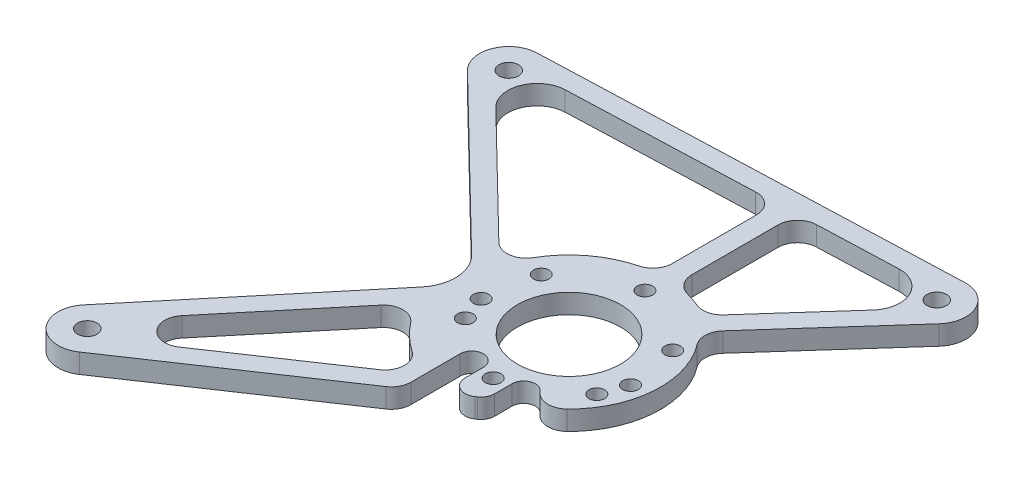
SolidWorks part; units mm, degrees
material "7050-T73510"
ref_plane "Płaszczyzna przednia" through (0, 0, 0) normal (0, 0, 1) x (1, 0, 0)
ref_plane "Płaszczyzna górna" through (0, 0, 0) normal (0, 1, 0) x (1, 0, 0)
ref_plane "Płaszczyzna prawa" through (0, 0, 0) normal (1, 0, 0) x (0, 0, -1)
sketch "Szkic3" plane through (0, 0, 0) normal (0, 1, 0) x (1, 0, 0)
  line L1 (-1915.5489, -140.9908) -> (-1703.3489, -133.2209)
  line L2 (-1750, -223.5762) -> (-1691.6125, -158.2029)
  line L3 (-1899.9755, -391.673) -> (-1768.1213, -302.9041)
  line L5 (-1842.3877, -247.6752) -> (-1925.468, -166.7241)
  line L10 (-1919.8833, -369.6363) -> (-1840.9708, -274.7914)
  line L11 (-1685.3, -117.9) -> (-1702.8, -148.2109) construction
  line L12 (-1507.3807, -117.9) -> (-1863.2193, -117.9) construction
  line L13 (-2061.0869, -130) -> (-1798.9131, -130) construction
  line L14 (-1915, -155.9808) -> (-1930, -130) construction
  circle A2 centre (-1930, -130) radius 12.5
  circle A3 centre (-1685.3, -117.9) radius 12.5
  arc A5 (-1750, -223.5762) -> (-1768.1213, -302.9041) centre (-1782, -258) cw
  circle A6 centre (-1782, -258) radius 26.5
  arc A8 (-1925.468, -166.7241) -> (-1915.5489, -140.9908) centre (-1915, -155.9808) cw
  arc A9 (-1691.6125, -158.2029) -> (-1703.3489, -133.2209) centre (-1702.8, -148.2109) ccw
  circle A10 centre (-1930, -400) radius 12.5
  arc A11 (-1919.8833, -369.6363) -> (-1899.9755, -391.673) centre (-1908.3525, -379.2301) ccw
  arc A20 (-1840.9708, -274.7914) -> (-1842.3877, -247.6752) centre (-1856.3451, -261.9997) ccw
  point P17 (-1685.3, -117.9)
  point P25 (-1930, -130)
  dimension "D4" = 47
  dimension "D7" = 25
  dimension "D10" = 25
  dimension "D11" = 53
  dimension "D12" = 15
  dimension "D5" = 1782
  dimension "D18" = 25
  dimension "D20" = 15
  dimension "D13" = 15
  dimension "D19" = 30
  dimension "D23" = 270
  dimension "D27" = 30
  dimension "D3" = 1930
  dimension "D14" = 130
  dimension "D15" = 1930
  dimension "D21" = 20
  dimension "D28" = 121.2301
  dimension "D6" = 258
  dimension "D8" = 117.9
  dimension "D9" = 1685.3
  dimension "D16" = 32
  dimension "D17" = 74.3451
  dimension "D22" = 60
  dimension "D24" = 35
  dimension "D25" = 117.9755
  dimension "D26" = 137.8833
  dimension "D29" = 60
extrude "Dodanie-wyciągnięcie1" add sketch "Szkic3" along normal blind 10
hole_wizard "Otwór1" positions "Szkic4" profile "Szkic5" legacy end condition up to next
sketch "Szkic4" plane through (0, 0, 0) normal (0, -1, 0) x (-1, 0, 0)
  circle A0 centre (1782, -258) radius 26.5 construction
  circle A1 centre (1782, -258) radius 26.5
  point P0 (1782, -219)
  dimension "D1" = 39
sketch "Szkic5" plane through (-1782, 0, 219) normal (1, 0, 0) x (0, 0, -1)
  line L0 (0, 0) -> (0, 10.001)
  line L1 (0, 10.001) -> (4, 10.001)
  line L2 (4, 10.001) -> (4, 0)
  line L3 (4, 0) -> (0, 0)
  line L4 (0, 110) -> (0, -10) construction
  dimension "Średnica" = 8
  dimension "Głębokość" = 10.001
pattern_circular "Szyk kołowy1" count 18 over 360 about axis through (-1782, 10, 258) along (0, -1, 0) skipping 1, 2, 4, 7, 8, 10, 11, 14, 16, 17 of "Otwór1"
hole_wizard "Otwór2" positions "Szkic8" profile "Szkic9" legacy
sketch "Szkic8" plane through (0, 0, 0) normal (0, -1, 0) x (-1, 0, 0)
  arc A0 (1703.3489, -133.2209) -> (1691.6125, -158.2029) centre (1702.8, -148.2109) ccw construction
  point P0 (1702.8, -148.2109)
sketch "Szkic9" plane through (-1702.8, 0, 148.2109) normal (1, 0, 0) x (0, 0, -1)
  line L0 (0, 0) -> (0, 100)
  line L1 (0, 100) -> (5, 100)
  line L2 (5, 100) -> (5, 0)
  line L3 (5, 0) -> (0, 0)
  line L4 (0, 110) -> (0, -10) construction
  dimension "Średnica" = 10
  dimension "Głębokość" = 100
hole_wizard "Otwór3" positions "Szkic10" profile "Szkic11" legacy
sketch "Szkic10" plane through (0, 0, 0) normal (0, -1, 0) x (-1, 0, 0)
  arc A0 (1925.468, -166.7241) -> (1915.5489, -140.9908) centre (1915, -155.9808) ccw construction
  point P0 (1915, -155.9808)
sketch "Szkic11" plane through (-1915, 0, 155.9808) normal (1, 0, 0) x (0, 0, -1)
  line L0 (0, 0) -> (0, 100)
  line L1 (0, 100) -> (5, 100)
  line L2 (5, 100) -> (5, 0)
  line L3 (5, 0) -> (0, 0)
  line L4 (0, 110) -> (0, -10) construction
  dimension "Średnica" = 10
  dimension "Głębokość" = 100
hole_wizard "Otwór4" positions "Szkic12" profile "Szkic13" legacy end condition up to next
sketch "Szkic12" plane through (0, 0, 0) normal (0, -1, 0) x (-1, 0, 0)
  arc A0 (1899.9755, -391.673) -> (1919.8833, -369.6363) centre (1908.3525, -379.2301) ccw construction
  point P0 (1908.3525, -379.2301)
sketch "Szkic13" plane through (-1908.3525, 0, 379.2301) normal (1, 0, 0) x (0, 0, -1)
  line L0 (0, 0) -> (0, 10)
  line L1 (0, 10) -> (5, 10)
  line L2 (5, 10) -> (5, 0)
  line L3 (5, 0) -> (0, 0)
  line L4 (0, 110) -> (0, -10) construction
  dimension "Średnica" = 10
  dimension "Głębokość" = 10
sketch "Szkic14" plane through (0, 0, 0) normal (0, -1, 0) x (-1, 0, 0)
  line L0 (1830.3878, -245.4055) -> (1901.7597, -175.8627)
  line L1 (1787, -208.2506) -> (1787, -146.2906)
  line L2 (1787, -146.2906) -> (1891.8406, -150.1294)
  line L3 (1777, -208.2506) -> (1777, -145.9244)
  line L4 (1777, -145.9244) -> (1726.4495, -144.0735)
  line L5 (1756.0056, -215.2883) -> (1714.7132, -169.0554)
  line L6 (1915.5489, -140.9908) -> (1703.3489, -133.2209) construction
  line L7 (1889.8509, -349.1755) -> (1834.501, -282.6505)
  line L8 (1750, -223.5762) -> (1691.6125, -158.2029) construction
  line L9 (1876.5791, -363.8666) -> (1800.8187, -312.8621)
  line L10 (1925.468, -166.7241) -> (1842.3877, -247.6752) construction
  line L11 (1899.9755, -391.673) -> (1768.1213, -302.9041) construction
  line L12 (1919.8833, -369.6363) -> (1840.9708, -274.7914) construction
  arc A0 (1830.3878, -245.4055) -> (1787, -208.2506) centre (1782, -258) ccw
  arc A1 (1901.7597, -175.8627) -> (1891.8406, -150.1294) centre (1891.2917, -165.1194) ccw
  arc A2 (1714.7132, -169.0554) -> (1726.4495, -144.0735) centre (1725.9007, -159.0634) cw
  arc A3 (1756.0056, -215.2883) -> (1777, -208.2506) centre (1782, -258) cw
  circle A4 centre (1782, -258) radius 26.5 construction
  circle A5 centre (1782, -258) radius 26.5 construction
  arc A8 (1834.501, -282.6505) -> (1800.8187, -312.8621) centre (1782, -258) cw
  arc A9 (1889.8509, -349.1755) -> (1876.5791, -363.8666) centre (1882.1637, -355.5714) cw
  dimension "D2" = 50
  dimension "D3" = 50
  dimension "D11" = 58
  dimension "D14" = 10
  dimension "D9" = 15
  dimension "D10" = 15
  dimension "D1" = 10
  dimension "D4" = 10
  dimension "D5" = 10
  dimension "D6" = 5
  dimension "D7" = 10
  dimension "D8" = 10
  dimension "D12" = 10
  dimension "D13" = 10
extrude "Wytnij-wyciągnięcie1" cut sketch "Szkic14" against normal through all
fillet "Zaokrąglenie1" radius 10 10 edges at (-1756.0056, 5, 215.2883) (-1787, 5, 208.2506) (-1777, 5, 208.2506) (-1787, 5, 146.2906) (-1777, 5, 145.9244) (-1834.501, 5, 282.6505) (-1768.1213, 5, 302.9041) (-1830.3878, 5, 245.4055) (-1800.8187, 5, 312.8621) (-1750, 5, 223.5762)
hole_wizard "Otwór5" positions "Szkic15" profile "Szkic16" legacy end condition up to next
sketch "Szkic15" plane through (0, 0, 0) normal (0, -1, 0) x (-1, 0, 0)
  point P0 (1795.3388, -294.648)
  point P2 (1768.6612, -294.648)
sketch "Szkic16" plane through (-1795.3388, 0, 294.648) normal (1, 0, 0) x (0, 0, -1)
  line L0 (0, 0) -> (0, 10)
  line L1 (0, 10) -> (5, 10)
  line L2 (5, 10) -> (5, 0)
  line L3 (5, 0) -> (0, 0)
  line L4 (0, 110) -> (0, -10) construction
  dimension "Średnica" = 10
  dimension "Głębokość" = 10
sketch "Szkic18" plane through (0, 0, 0) normal (0, -1, 0) x (-1, 0, 0)
  line L0 (1762.6612, -294.648) -> (1762.6612, -300.837)
  line L1 (1774.6612, -294.648) -> (1774.6612, -307.3071)
  line L2 (1789.3388, -294.648) -> (1789.3388, -317.1885)
  line L3 (1801.3388, -294.648) -> (1801.3388, -325.2673)
  line L4 (1899.9755, -391.673) -> (1769.2842, -303.6871) construction
  line L5 (1899.9755, -391.673) -> (1769.2842, -303.6871) construction
  line L6 (1801.3388, -325.2673) -> (1789.3388, -317.1885)
  line L7 (1774.6612, -307.3071) -> (1769.2842, -303.6871)
  arc A0 (1762.6612, -294.648) -> (1774.6612, -294.648) centre (1768.6612, -294.648) cw
  arc A1 (1789.3388, -294.648) -> (1801.3388, -294.648) centre (1795.3388, -294.648) cw
  circle A2 centre (1768.6612, -294.648) radius 5 construction
  circle A3 centre (1795.3388, -294.648) radius 5 construction
  arc A5 (1769.2842, -303.6871) -> (1766.9102, -302.5118) centre (1763.6996, -311.9823) ccw
  arc A6 (1766.9102, -302.5118) -> (1762.6612, -300.837) centre (1782, -258) cw
  circle A13 centre (1782, -258) radius 26.5 construction
  dimension "D1" = 6
  dimension "D2" = 6
  dimension "D3" = 10
extrude "Wytnij-wyciągnięcie2" cut sketch "Szkic18" against normal blind 10
fillet "Zaokrąglenie2" radius 10 2 edges at (-1762.6612, 5, 300.837) (-1801.3388, 5, 325.2673)
fillet "Zaokrąglenie7" radius 7 2 edges at (-1789.3388, 5, 317.1885) (-1774.6612, 5, 307.3071)
